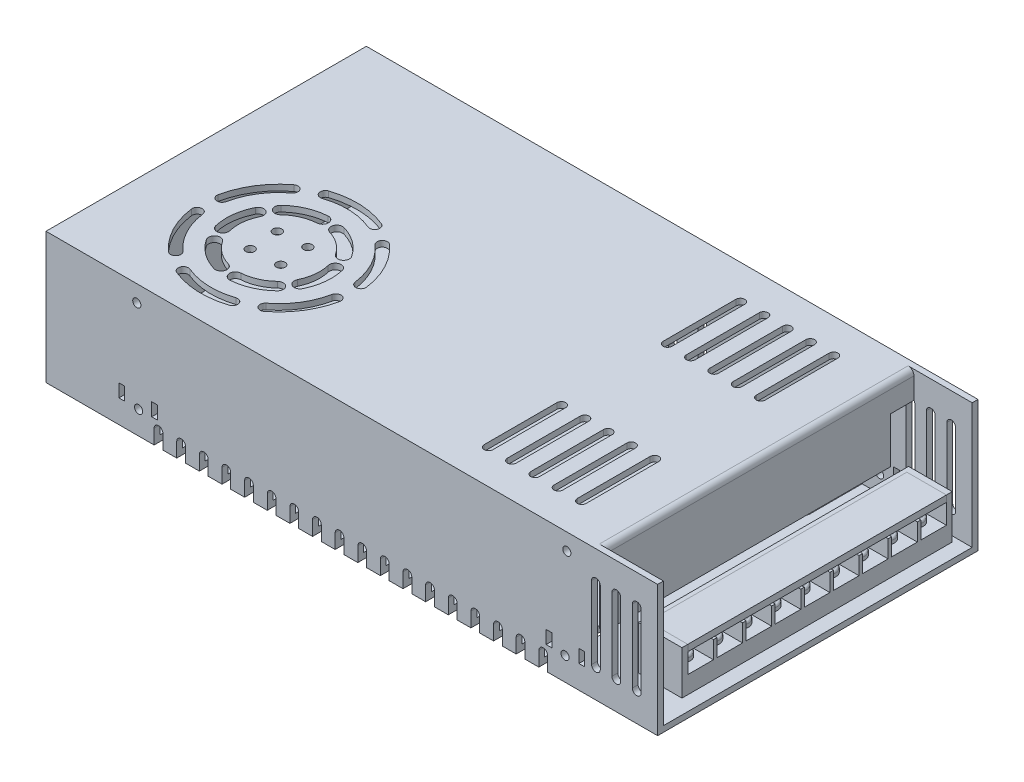
SolidWorks part; units mm, degrees
ref_plane "Front Plane" through (0, 0, 0) normal (0, 0, 1) x (1, 0, 0)
ref_plane "Top Plane" through (0, 0, 0) normal (0, 1, 0) x (1, 0, 0)
ref_plane "Right Plane" through (0, 0, 0) normal (1, 0, 0) x (0, 0, -1)
sketch "Sketch1" plane through (0, 0, 0) normal (0, 1, 0) x (1, 0, 0)
  line L1 (-105, -55) -> (105, -55)
  line L2 (-105, -55) -> (-105, 55)
  line L3 (-105, 55) -> (105, 55)
  line L4 (105, -55) -> (105, 55)
  line L5 (-105, -55) -> (105, 55) construction
  line L6 (-105, 55) -> (105, -55) construction
  point P0 (0, 0)
extrude "Boss-Extrude1" add sketch "Sketch1" along normal blind 45
shell "Shell1" thickness 2
sketch "Sketch2" plane through (0, 45, 0) normal (0, 1, 0) x (1, 0, 0)
  line L0 (105, 53) -> (85, 53)
  line L1 (105, 53) -> (105, -53)
  line L2 (105, -53) -> (85, -53)
  line L3 (85, -53) -> (85, 53)
extrude "Cut-Extrude1" cut sketch "Sketch2" against normal blind 5
sketch "Sketch3" plane through (0, 45, 0) normal (0, 1, 0) x (1, 0, 0)
  line L1 (85, 53) -> (83, 53)
  line L2 (85, 53) -> (85, -53.0593)
  line L3 (85, -53.0593) -> (83, -53.0593)
  line L4 (83, 53) -> (83, -53.0593)
extrude "Boss-Extrude2" add sketch "Sketch3" against normal blind 25
fillet "Fillet1" radius 2 1 edges at (85, 45, 0)
sketch "Sketch5" plane through (0, 45, 0) normal (0, 1, 0) x (1, 0, 0)
  line L0 (67.1672, 43.2346) -> (67.1672, 18.2346) construction
  line L1 (68.6672, 43.2346) -> (68.6672, 18.2346)
  line L2 (65.6672, 43.2346) -> (65.6672, 18.2346)
  arc A0 (68.6672, 43.2346) -> (65.6672, 43.2346) centre (67.1672, 43.2346) ccw
  arc A1 (65.6672, 18.2346) -> (68.6672, 18.2346) centre (67.1672, 18.2346) ccw
  point P2 (67.1672, 30.7346)
extrude "Cut-Extrude2" cut sketch "Sketch5" against normal blind 10
pattern_linear "LPattern1" count 5 spacing 8 along (-1, 0, 0) of "Cut-Extrude2"
mirror "Mirror1" about plane through (0, 0, 0) normal (0, 0, 1) of "Cut-Extrude2", "LPattern1"
sketch "Sketch6" plane through (0, 45, 0) normal (0, 1, 0) x (1, 0, 0)
  arc A0 (-74.3347, -12.8926) -> (-75.5496, -23.7696) centre (-60, -20) ccw construction
  arc A1 (-76.1266, -12.0042) -> (-77.4933, -24.2408) centre (-60, -20) ccw
  arc A2 (-72.5429, -13.781) -> (-73.6059, -23.2984) centre (-60, -20) ccw
  arc A3 (-72.5429, -13.781) -> (-76.1266, -12.0042) centre (-74.3347, -12.8926) ccw
  arc A4 (-77.4933, -24.2408) -> (-73.6059, -23.2984) centre (-75.5496, -23.7696) ccw
  point P3 (-75.9011, -18.224)
extrude "Cut-Extrude3" cut sketch "Sketch6" against normal blind 10
sketch "Sketch7" plane through (0, 45, 0) normal (0, 1, 0) x (1, 0, 0)
  circle A0 centre (-60, -20) radius 1
extrude "Boss-Extrude3" add sketch "Sketch7" along normal blind 10
pattern_circular "CirPattern1" count 6 over 360 about axis through (-60, 0, 20) along (0, 1, 0) of "Cut-Extrude3"
sketch "Sketch8" plane through (0, 45, 0) normal (0, 1, 0) x (1, 0, 0)
  arc A0 (-67.9112, 3.8426) -> (-50.3064, 3.1752) centre (-60, -20) cw construction
  arc A1 (-49.6312, 4.7897) -> (-68.4623, 5.5035) centre (-60, -20) ccw
  arc A2 (-50.9817, 1.5607) -> (-67.3601, 2.1816) centre (-60, -20) ccw
  arc A3 (-50.9817, 1.5607) -> (-49.6312, 4.7897) centre (-50.3064, 3.1752) ccw
  arc A4 (-68.4623, 5.5035) -> (-67.3601, 2.1816) centre (-67.9112, 3.8426) ccw
  point P4 (-59.0484, 5.1028)
extrude "Cut-Extrude4" cut sketch "Sketch8" against normal blind 10
pattern_circular "CirPattern2" count 6 over 360 about axis through (-60, 0, 20) along (0, 1, 0) of "Cut-Extrude4"
sketch "Sketch9" plane through (0, 45, 0) normal (0, 1, 0) x (1, 0, 0)
  circle A0 centre (-65.2517, -15.3391) radius 1.5
extrude "Cut-Extrude5" cut sketch "Sketch9" against normal blind 10
pattern_circular "CirPattern3" count 4 over 360 about axis through (-60, 0, 20) along (0, 1, 0) of "Cut-Extrude5"
sketch "Sketch11" plane through (0, 45, 0) normal (0, 1, 0) x (1, 0, 0)
  circle A0 centre (-60.782, -15.3391) radius 10.5536
extrude "Cut-Extrude7" cut sketch "Sketch11" along normal blind 34
sketch "Sketch12" plane through (0, 0, 55) normal (0, 0, 1) x (1, 0, 0)
  line L0 (97.8103, 34.8113) -> (97.8103, 9.8113) construction
  line L1 (99.3103, 34.8113) -> (99.3103, 9.8113)
  line L2 (96.3103, 34.8113) -> (96.3103, 9.8113)
  arc A0 (99.3103, 34.8113) -> (96.3103, 34.8113) centre (97.8103, 34.8113) ccw
  arc A1 (96.3103, 9.8113) -> (99.3103, 9.8113) centre (97.8103, 9.8113) ccw
  point P2 (97.8103, 22.3113)
extrude "Cut-Extrude8" cut sketch "Sketch12" against normal blind 10
pattern_linear "LPattern2" count 3 spacing 7 along (-1, 0, 0) of "Cut-Extrude8"
sketch "Sketch14" plane through (0, 0, 45) normal (0, 0, 1) x (1, 0, 0)
  line L3 (85, 20) -> (85, 35.7249)
  line L4 (83, 36.0736) -> (83, 20)
  line L5 (83, 20) -> (85, 20)
  line L6 (85, 20) -> (85, 35.7249)
  line L7 (83, 36.0736) -> (83, 20)
  line L8 (83, 20) -> (85, 20)
  arc A1 (85, 35.7249) -> (83, 36.0736) centre (83.8103, 34.8113) ccw
  arc A2 (85, 35.7249) -> (83, 36.0736) centre (83.8103, 34.8113) ccw
  dimension "D1" = 0
extrude "Boss-Extrude4" add sketch "Sketch14" along normal up to surface (98 mm away)
sketch "Sketch15" plane through (0, 0, 55) normal (0, 0, 1) x (1, 0, 0)
  line L1 (77.9695, 12.4645) -> (79.9695, 12.4645)
  line L2 (77.9695, 12.4645) -> (77.9695, 7.9645)
  line L3 (77.9695, 7.9645) -> (79.9695, 7.9645)
  line L4 (79.9695, 12.4645) -> (79.9695, 7.9645)
  line L5 (66.7101, 12.4645) -> (68.7101, 12.4645)
  line L6 (66.7101, 12.4645) -> (66.7101, 7.9645)
  line L7 (66.7101, 7.9645) -> (68.7101, 7.9645)
  line L8 (68.7101, 12.4645) -> (68.7101, 7.9645)
  circle A0 centre (73.2101, 7.9645) radius 1.4
  circle A1 centre (73.8281, 39.2835) radius 1.4
  dimension "D1" = 4.5
extrude "Cut-Extrude9" cut sketch "Sketch15" against normal blind 12
mirror "Mirror2" about plane through (0, 0, 0) normal (1, 0, 0) of "Cut-Extrude9"
mirror "Mirror3" about plane through (0, 0, 0) normal (0, 0, 1) of "Mirror2", "Cut-Extrude9", "Cut-Extrude8", "LPattern2"
sketch "Sketch16" plane through (0, 0, -55) normal (0, 0, -1) x (-1, 0, 0)
  line L0 (-12.3422, 34.8113) -> (-12.3422, 9.8113) construction
  line L1 (-10.8422, 34.8113) -> (-10.8422, 9.8113)
  line L2 (-13.8422, 34.8113) -> (-13.8422, 9.8113)
  line L3 (-2.1571, 34.8113) -> (-2.1571, 9.8113) construction
  line L4 (-0.6571, 34.8113) -> (-0.6571, 9.8113)
  line L5 (-3.6571, 34.8113) -> (-3.6571, 9.8113)
  line L7 (10.8422, 16.5509) -> (28.8422, 16.5509)
  line L8 (10.8422, 16.5509) -> (10.8422, 7.5509)
  line L9 (10.8422, 7.5509) -> (28.8422, 7.5509)
  line L10 (28.8422, 16.5509) -> (28.8422, 7.5509)
  arc A0 (-10.8422, 34.8113) -> (-13.8422, 34.8113) centre (-12.3422, 34.8113) ccw
  arc A1 (-13.8422, 9.8113) -> (-10.8422, 9.8113) centre (-12.3422, 9.8113) ccw
  arc A2 (-0.6571, 34.8113) -> (-3.6571, 34.8113) centre (-2.1571, 34.8113) ccw
  arc A3 (-3.6571, 9.8113) -> (-0.6571, 9.8113) centre (-2.1571, 9.8113) ccw
  point P2 (-12.3422, 22.3113)
  point P9 (-2.1571, 22.3113)
extrude "Cut-Extrude10" cut sketch "Sketch16" against normal blind 12
sketch "Sketch17" plane through (0, 0, 0) normal (0, -1, 0) x (1, 0, 0)
  line L0 (65.7103, -55) -> (65.7103, -35) construction
  line L1 (105, -55) -> (-105, -55) construction
  line L2 (64.2103, -55) -> (64.2103, -35)
  line L3 (67.2103, -55) -> (67.2103, -35)
  arc A0 (64.2103, -55) -> (67.2103, -55) centre (65.7103, -55) ccw
  arc A1 (67.2103, -35) -> (64.2103, -35) centre (65.7103, -35) ccw
  point P4 (65.7103, -45)
extrude "Cut-Extrude11" cut sketch "Sketch17" against normal blind 5
pattern_linear "LPattern3" count 18 spacing 7.77 along (-1, 0, 0) of "Cut-Extrude11"
mirror "Mirror4" about plane through (0, 0, 0) normal (0, 0, 1) of "Cut-Extrude11", "LPattern3"
sketch "Sketch18" plane through (0, 0, -55) normal (0, 0, -1) x (-1, 0, 0)
  line L0 (-64.2103, 5) -> (-67.2103, 5) construction
  circle A0 centre (-65.7103, 5) radius 1.5
extrude "Cut-Extrude12" cut sketch "Sketch18" against normal up to surface (110 mm away) up to face at (-78.9695, 10.2145, 55)
pattern_linear "LPattern4" count 18 spacing 7.77 along (-1, 0, 0) of "Cut-Extrude12"
sketch "Sketch20" plane through (85, 0, 0) normal (1, 0, 0) x (0, 0, -1)
  line L0 (-53, 2) -> (53, 2) construction
  line L1 (40.3547, 8) -> (49.1547, 8)
  line L2 (39.7547, 8) -> (39.7547, 2)
  line L3 (39.7547, 2) -> (49.7547, 2)
  line L4 (49.7547, 8) -> (49.7547, 2)
  line L5 (39.7547, 8) -> (39.7547, 14)
  line L6 (39.7547, 14) -> (40.3547, 14)
  line L7 (40.3547, 14) -> (40.3547, 8)
  line L8 (49.7547, 8) -> (49.7547, 14)
  line L9 (49.7547, 14) -> (49.1547, 14)
  line L10 (49.1547, 14) -> (49.1547, 8)
extrude "Boss-Extrude5" add sketch "Sketch20" along normal blind 15
pattern_linear "LPattern5" count 9 spacing 10 along (0, 0, 1) of "Boss-Extrude5"
sketch "Sketch21" plane through (0, 2, 0) normal (0, 1, 0) x (1, 0, 0)
  line L1 (86.4205, -39.6453) -> (100, -39.6453)
  line L2 (85, -39.6453) -> (85, -41.6453)
  line L3 (85, -41.6453) -> (100, -41.6453)
  line L4 (100, -39.6453) -> (100, -41.6453)
  line L5 (100, 49.1547) -> (86.4205, 49.1547)
  line L6 (100, 49.1547) -> (100, 51.1547)
  line L7 (100, 51.1547) -> (85, 51.1547)
  line L8 (85, 49.1547) -> (85, 51.1547)
  line L10 (85, 49.1547) -> (85, -39.6453)
  line L12 (86.4205, 49.1547) -> (86.4205, -39.6453)
extrude "Boss-Extrude6" add sketch "Sketch21" along normal blind 15
sketch "Sketch22" plane through (86.4205, 0, 0) normal (1, 0, 0) x (0, 0, -1)
  line L0 (49.1547, 17) -> (49.1547, 8) construction
  line L1 (-39.6453, 17) -> (49.1547, 17)
  line L2 (-39.6453, 17) -> (-39.6453, 14.8)
  line L3 (-39.6453, 14.8) -> (49.1547, 14.8)
  line L4 (49.1547, 17) -> (49.1547, 14.8)
extrude "Boss-Extrude7" add sketch "Sketch22" along normal up to surface (13.5795 mm away) separate body up to face at (100, 11, -4.7547)
sketch "Sketch23" plane through (0, 8, 0) normal (0, 1, 0) x (1, 0, 0)
  circle A0 centre (93.3652, 44.7637) radius 3
extrude "Boss-Extrude8" add sketch "Sketch23" along normal blind 2
fillet "Fillet2" radius 0.8 1 edges at (93.3652, 10, -41.7637)
pattern_linear "LPattern6" count 9 spacing 10 along (0, 0, 1) of "Fillet2", "Boss-Extrude8"
